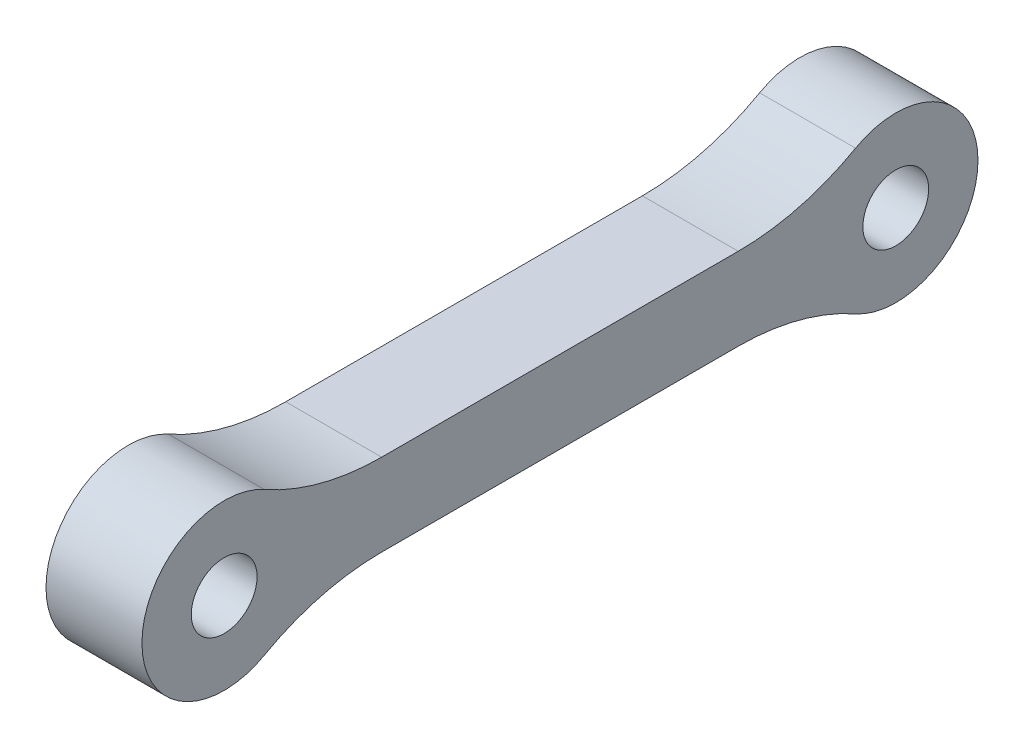
SolidWorks part; units mm, degrees
material "Tough 2000"
ref_plane "Front Plane" through (0, 0, 0) normal (0, 0, 1) x (1, 0, 0)
ref_plane "Top Plane" through (0, 0, 0) normal (0, 1, 0) x (1, 0, 0)
ref_plane "Right Plane" through (0, 0, 0) normal (1, 0, 0) x (0, 0, -1)
sketch "Sketch1" plane through (0, 0, 0) normal (1, 0, 0) x (0, 0, -1)
  line L2 (18, 1.7143) -> (25.0308, 1.7143)
  line L3 (18, 1.7143) -> (2.9692, 1.7143)
  line L5 (18, -1.7143) -> (25.0308, -1.7143)
  line L6 (18, -1.7143) -> (2.9692, -1.7143)
  arc A0 (25.0308, -1.7143) -> (25.0308, 1.7143) centre (28, 0) ccw
  arc A1 (2.9692, 1.7143) -> (2.9692, -1.7143) centre (0, 0) ccw
  circle A2 centre (0, 0) radius 1.3714
  circle A3 centre (28, 0) radius 1.3714
  dimension "D1" = 28
  dimension "D2" = 3.4286
  dimension "D3" = 3.4286
extrude "Boss-Extrude1" add sketch "Sketch1" along normal blind 4
fillet "Fillet1" radius 10 4 edges at (2, 1.7143, -2.9692) (2, -1.7143, -2.9692) (2, -1.7143, -25.0308) (2, 1.7143, -25.0308)
